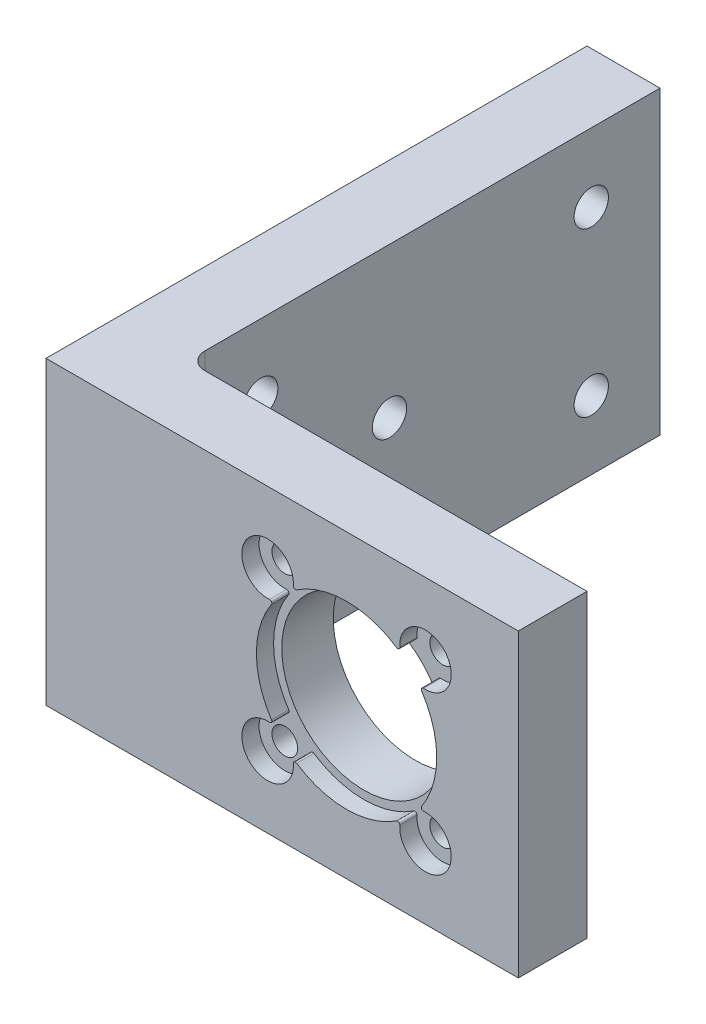
SolidWorks part; units mm, degrees
ref_plane "Piano frontale" through (0, 0, 0) normal (0, 0, 1) x (1, 0, 0)
ref_plane "Piano superiore" through (0, 0, 0) normal (0, 1, 0) x (1, 0, 0)
ref_plane "Piano destro" through (0, 0, 0) normal (1, 0, 0) x (0, 0, -1)
sketch "Sketch1" plane through (0, 0, 0) normal (0, 0, 1) x (1, 0, 0)
  line L0 (0, 17.5) -> (55, 17.5) construction
  line L1 (0, 0) -> (55, 0)
  line L2 (0, 0) -> (0, 35)
  line L3 (0, 35) -> (55, 35)
  line L4 (55, 0) -> (55, 35)
  line L5 (27.5, 35) -> (27.5, 0) construction
  line L6 (35, 17.5) -> (44.1924, 26.6924) construction
  line L7 (35, 17.5) -> (44.1924, 8.3076) construction
  line L8 (35, 17.5) -> (35, 0) construction
  line L9 (35, 17.5) -> (25.8076, 8.3076) construction
  line L10 (35, 17.5) -> (25.8076, 26.6924) construction
  circle A0 centre (35, 17.5) radius 9.55
  circle A1 centre (35, 17.5) radius 13 construction
  circle A2 centre (44.1924, 26.6924) radius 1.5
  circle A3 centre (44.1924, 8.3076) radius 1.5
  circle A4 centre (25.8076, 8.3076) radius 1.5
  circle A5 centre (25.8076, 26.6924) radius 1.5
  circle A6 centre (35, 17.5) radius 16 construction
  dimension "D2" = 19.1
  dimension "D4" = 26
  dimension "D6" = 3
  dimension "D7" = 17.5
  dimension "D9" = 32
  dimension "D1" = 55
  dimension "D3" = 20
  dimension "D5" = 45
  dimension "D8" = 35
extrude "Boss-Extrude3" add sketch "Sketch1" along normal blind 6
sketch "Sketch4" plane through (0, 0, 6) normal (0, 0, 1) x (1, 0, 0)
  line L0 (35, 17.5) -> (35, 34.7569) construction
  line L1 (35, 17.5) -> (35, 0) construction
  line L2 (0, 0) -> (55, 0) construction
  line L3 (35, 17.5) -> (0, 17.5) construction
  line L4 (0, 35) -> (0, 0) construction
  line L6 (0, 35) -> (55, 35)
  line L7 (0, 35) -> (0, 0)
  line L8 (0, 0) -> (55, 0)
  line L9 (55, 35) -> (55, 0)
  arc A0 (28.7994, 26.4708) -> (26.0292, 23.7006) centre (25.8076, 26.6924) ccw
  arc A1 (28.7994, 8.5292) -> (26.0292, 11.2994) centre (25.8076, 8.3076) cw
  arc A2 (41.2006, 8.5292) -> (43.9708, 11.2994) centre (44.1924, 8.3076) ccw
  arc A3 (41.2006, 26.4708) -> (43.9708, 23.7006) centre (44.1924, 26.6924) cw
  arc A4 (26.2558, 23.3129) -> (26.2558, 11.6871) centre (35, 17.5) ccw
  arc A5 (40.8129, 26.2442) -> (29.1871, 26.2442) centre (35, 17.5) ccw
  arc A6 (43.7442, 11.6871) -> (43.7442, 23.3129) centre (35, 17.5) ccw
  arc A7 (29.1871, 8.7558) -> (40.8129, 8.7558) centre (35, 17.5) ccw
  arc A8 (26.2558, 11.6871) -> (26.0292, 11.2994) centre (26.0476, 11.5487) cw
  arc A9 (29.1871, 8.7558) -> (28.7994, 8.5292) centre (29.0487, 8.5476) ccw
  arc A10 (40.8129, 8.7558) -> (41.2006, 8.5292) centre (40.9513, 8.5476) cw
  arc A11 (43.7442, 11.6871) -> (43.9708, 11.2994) centre (43.9524, 11.5487) ccw
  arc A12 (43.7442, 23.3129) -> (43.9708, 23.7006) centre (43.9524, 23.4513) cw
  arc A13 (40.8129, 26.2442) -> (41.2006, 26.4708) centre (40.9513, 26.4524) ccw
  arc A14 (29.1871, 26.2442) -> (28.7994, 26.4708) centre (29.0487, 26.4524) cw
  arc A15 (26.2558, 23.3129) -> (26.0292, 23.7006) centre (26.0476, 23.4513) ccw
  dimension "D1" = 6
  dimension "D2" = 21
  dimension "D3" = 0.25
extrude "Boss-Extrude5" add sketch "Sketch4" along normal blind 2
sketch "Sketch8" plane through (0, 0, 0) normal (0, 0, -1) x (-1, 0, 0)
  line L0 (-55, 35) -> (0, 35) construction
  line L1 (-8.5, 35) -> (0, 35)
  line L3 (-8.5, 0) -> (0, 0)
  line L4 (0, 35) -> (0, 0)
  line L6 (0, 35) -> (0, 0) construction
  line L7 (-8.5, 35) -> (-8.5, 0)
  line L9 (0, 25) -> (0, 10)
  line L11 (-18.1947, 25) -> (-18.1947, 24.9954)
  line L13 (0, 35) -> (-8.5, 35)
  line L14 (0, 35) -> (0, 0)
  line L15 (0, 0) -> (-8.5, 0)
  dimension "D4" = 18.1947
  dimension "D6" = 8.5
extrude "Boss-Extrude6" add sketch "Sketch8" along normal blind 55
sketch "Sketch9" plane through (0, 0, 0) normal (-1, 0, 0) x (0, 0, 1)
  line L0 (-55, 17.5) -> (8, 17.5) construction
  line L3 (-55, 0) -> (-55, 35) construction
  line L4 (8, 35) -> (8, 0) construction
  line L5 (-23.5, 35) -> (-23.5, 0) construction
  line L6 (8, 35) -> (-55, 35) construction
  line L7 (8, 0) -> (-55, 0) construction
  circle A3 centre (-47, 27) radius 2
  circle A4 centre (-47, 8) radius 2
  circle A5 centre (-8.5, 27) radius 2
  circle A6 centre (-8.5, 8) radius 2
  circle A7 centre (-23.5, 17.5) radius 2
  dimension "D1" = 4
  dimension "D4" = 4
  dimension "D7" = 4
  dimension "D2" = 8
  dimension "D3" = 8
  dimension "D5" = 8
  dimension "D6" = 16.5
extrude "Cut-Extrude1" cut sketch "Sketch9" against normal blind 8.5
fillet "Fillet1" radius 2 1 edges at (8.5, 17.5, 0)
